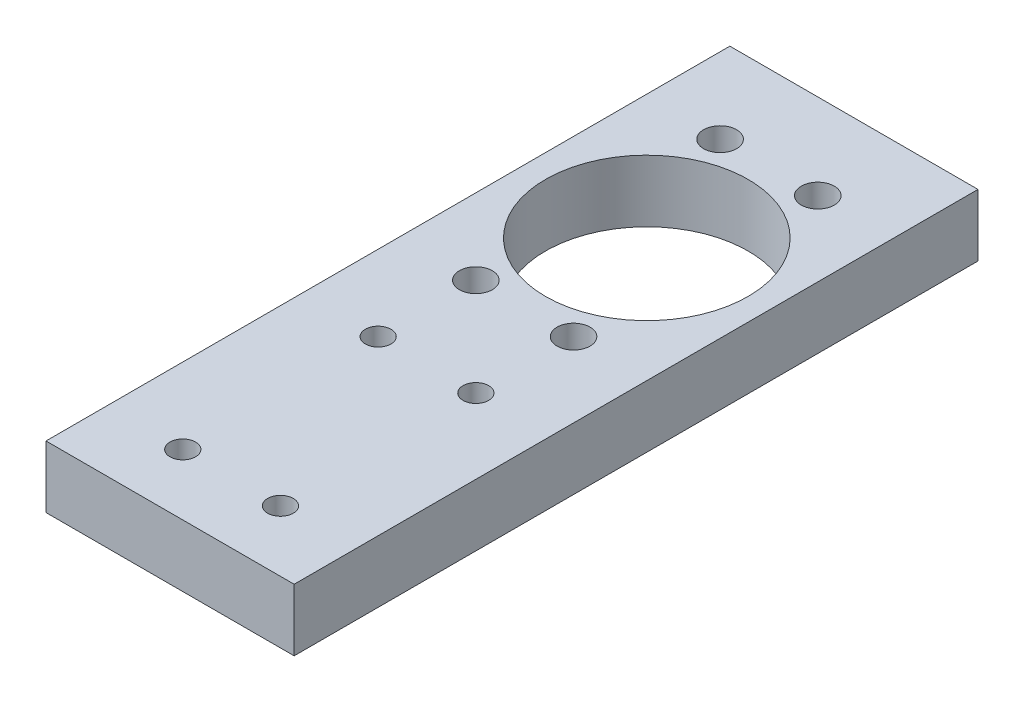
SolidWorks part; units mm, degrees
ref_plane "Front Plane" through (0, 0, 0) normal (0, 0, 1) x (1, 0, 0)
ref_plane "Top Plane" through (0, 0, 0) normal (0, 1, 0) x (1, 0, 0)
ref_plane "Right Plane" through (0, 0, 0) normal (1, 0, 0) x (0, 0, -1)
sketch "Sketch2" plane through (0, 0, 0) normal (0, 1, 0) x (1, 0, 0)
  line L1 (0, 0) -> (101.6, 0)
  line L2 (0, 0) -> (0, 280)
  line L3 (0, 280) -> (101.6, 280)
  line L4 (101.6, 0) -> (101.6, 280)
  dimension "D1" = 101.6
  dimension "D2" = 280
extrude "Boss-Extrude1" add sketch "Sketch2" along normal blind 25.4
sketch "Sketch3" plane through (0, 25.4, 0) normal (0, 1, 0) x (1, 0, 0)
  line L1 (0, 280) -> (51, 280)
  line L2 (0, 280) -> (0, 195)
  line L3 (0, 195) -> (51, 195)
  line L4 (51, 280) -> (51, 195)
  line L5 (31, 245) -> (71, 245)
  line L6 (31, 245) -> (31, 145)
  line L7 (31, 145) -> (71, 145)
  line L8 (71, 245) -> (71, 145)
  line L9 (31, 245) -> (71, 145) construction
  line L10 (31, 145) -> (71, 245) construction
  circle A0 centre (71, 245) radius 6.75
  circle A1 centre (31, 245) radius 6.75
  circle A2 centre (71, 145) radius 6.75
  circle A3 centre (31, 145) radius 6.75
  circle A4 centre (51, 195) radius 41.5
  dimension "D1" = 51
  dimension "D2" = 85
  dimension "D3" = 40
  dimension "D4" = 100
extrude "Cut-Extrude1" cut sketch "Sketch3" against normal blind 25.4 contours A1 | A0 | A4 | A2 | A3
sketch "Sketch4" plane through (0, 25.4, 0) normal (0, 1, 0) x (1, 0, 0)
  line L1 (0, 280) -> (51, 280)
  line L2 (0, 280) -> (0, 65)
  line L3 (0, 65) -> (51, 65)
  line L4 (51, 280) -> (51, 65)
  line L5 (31, 25) -> (71, 25)
  line L6 (31, 25) -> (31, 105)
  line L7 (31, 105) -> (71, 105)
  line L8 (71, 25) -> (71, 105)
  line L9 (31, 25) -> (71, 105) construction
  line L10 (31, 105) -> (71, 25) construction
  circle A0 centre (71, 105) radius 5.25
  circle A1 centre (31, 105) radius 5.25
  circle A2 centre (31, 25) radius 5.25
  circle A3 centre (71, 25) radius 5.25
  dimension "D1" = 51
  dimension "D2" = 215
  dimension "D3" = 40
  dimension "D4" = 80
extrude "Cut-Extrude2" cut sketch "Sketch4" against normal blind 25.4 contours A1 | A0 | A3 | A2
